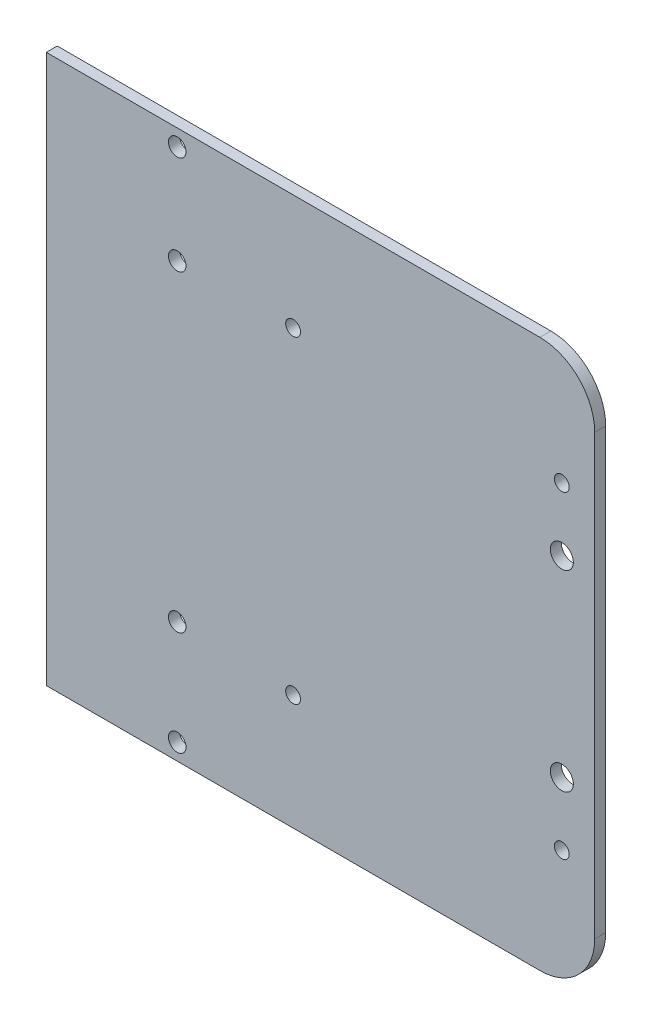
SolidWorks part; units mm, degrees
ref_plane "前视基准面" through (0, 0, 0) normal (0, 0, 1) x (1, 0, 0)
ref_plane "上视基准面" through (0, 0, 0) normal (0, 1, 0) x (1, 0, 0)
ref_plane "右视基准面" through (0, 0, 0) normal (1, 0, 0) x (0, 0, -1)
sketch "草图1" plane through (0, 0, 0) normal (0, 0, 1) x (1, 0, 0)
  line L0 (50, 0) -> (-50, 0) construction
  line L1 (-50, 50) -> (40, 50)
  line L2 (-50, 50) -> (-50, -50)
  line L3 (-50, -50) -> (40, -50)
  line L4 (50, 40) -> (50, -40)
  line L5 (-50, 50) -> (50, -50) construction
  line L6 (-50, -50) -> (50, 50) construction
  arc A2 (40, 50) -> (50, 40) centre (40, 40) cw
  arc A3 (50, -40) -> (40, -50) centre (40, -40) cw
  point P0 (0, 0)
  dimension "D6" = 10
  dimension "D1" = 100
  dimension "D2" = 100
extrude "凸台-拉伸1" add sketch "草图1" along normal blind 2
sketch "草图3" plane through (0, 0, 2) normal (0, 0, 1) x (1, 0, 0)
  line L0 (-50, 0) -> (50, 0) construction
  line L1 (-5, -50) -> (-5, 50) construction
  line L2 (19.5, -50) -> (19.5, 50) construction
  line L3 (44, -50) -> (44, 50) construction
  line L4 (50, -40) -> (50, 40)
  line L5 (40, 50) -> (-50, 50)
  line L6 (-50, 50) -> (-50, -50)
  line L7 (-50, -50) -> (40, -50)
  line L8 (50, -40) -> (50, 40)
  line L9 (40, 50) -> (-50, 50)
  line L10 (-50, 50) -> (-50, -50)
  line L11 (-50, -50) -> (40, -50)
  circle A0 centre (-5, -29) radius 1.35
  circle A1 centre (-5, 29) radius 1.35
  circle A2 centre (44, 29) radius 1.35
  circle A3 centre (44, -29) radius 1.35
  arc A6 (40, -50) -> (50, -40) centre (40, -40) ccw
  arc A7 (40, -50) -> (50, -40) centre (40, -40) ccw
  arc A8 (50, 40) -> (40, 50) centre (40, 40) ccw
  arc A9 (50, 40) -> (40, 50) centre (40, 40) ccw
  dimension "D3" = 2.7
  dimension "D4" = 58
  dimension "D5" = 49
  dimension "D2" = 6
  dimension "D1" = 0
extrude "切除-拉伸1" cut sketch "草图3" against normal through all contours A0 | A1 | A2 | A3
sketch "草图7" plane through (0, 0, 2) normal (0, 0, 1) x (1, 0, 0)
  line L0 (50, 0) -> (-50, 0) construction
  line L1 (44, 50) -> (44, -50) construction
  line L4 (50, -40) -> (50, 40)
  line L5 (40, 50) -> (-50, 50)
  line L6 (-50, 50) -> (-50, -50)
  line L7 (-50, -50) -> (40, -50)
  line L8 (50, -40) -> (50, 40)
  line L9 (40, 50) -> (-50, 50)
  line L10 (-50, 50) -> (-50, -50)
  line L11 (-50, -50) -> (40, -50)
  circle A0 centre (44, 17.5) radius 2.1
  circle A1 centre (44, -17.5) radius 2.1
  arc A4 (40, -50) -> (50, -40) centre (40, -40) ccw
  arc A5 (40, -50) -> (50, -40) centre (40, -40) ccw
  arc A6 (50, 40) -> (40, 50) centre (40, 40) ccw
  arc A7 (50, 40) -> (40, 50) centre (40, 40) ccw
  dimension "D3" = 4.2
  dimension "D4" = 35
  dimension "D2" = 6
  dimension "D1" = 0
extrude "切除-拉伸5" cut sketch "草图7" against normal blind 10 contours A0 | A1
sketch "草图8" plane through (0, 0, 0) normal (0, 0, -1) x (-1, 0, 0)
  line L0 (23.125, 52) -> (23.125, 24) construction
  line L1 (23.125, 24) -> (51, 24) construction
  line L2 (51, 24) -> (51, 52) construction
  line L3 (51, 52) -> (23.125, 52) construction
  line L4 (50, -50) -> (50, 50)
  line L5 (50, 50) -> (-40, 50)
  line L6 (-50, 40) -> (-50, -40)
  line L7 (-40, -50) -> (50, -50)
  line L8 (50, -50) -> (50, 50)
  line L9 (50, 50) -> (-40, 50)
  line L10 (-50, 40) -> (-50, -40)
  line L11 (-40, -50) -> (50, -50)
  line L12 (51, -52) -> (51, -23) construction
  line L13 (51, -23) -> (23.125, -23) construction
  line L14 (23.125, -23) -> (23.125, -52) construction
  line L15 (23.125, -52) -> (51, -52) construction
  line L16 (23.125, 52) -> (23.125, 24)
  line L17 (23.125, 24) -> (51, 24)
  line L18 (51, 24) -> (51, 52)
  line L19 (51, 52) -> (23.125, 52)
  line L20 (51, -52) -> (51, -23)
  line L21 (51, -23) -> (23.125, -23)
  line L22 (23.125, -23) -> (23.125, -52)
  line L23 (23.125, -52) -> (51, -52)
  circle A0 centre (26.125, 29) radius 1.6
  circle A1 centre (26.125, 47) radius 1.6
  arc A2 (-40, 50) -> (-50, 40) centre (-40, 40) ccw
  arc A3 (-50, -40) -> (-40, -50) centre (-40, -40) ccw
  arc A4 (-40, 50) -> (-50, 40) centre (-40, 40) ccw
  arc A5 (-50, -40) -> (-40, -50) centre (-40, -40) ccw
  circle A6 centre (26.125, -28) radius 1.6
  circle A7 centre (26.125, -47) radius 1.6
  dimension "D1" = 0
extrude "切除-拉伸6" cut sketch "草图8" against normal through all contours A7 | A6 | A0 | A1
sketch "草图9" plane through (0, 0, 0) normal (0, 0, -1) x (-1, 0, 0)
  line L0 (-31.975, -49.5062) -> (-25.625, -49.5062) construction
  line L1 (22.125, -23) -> (50, -23)
  line L2 (22.125, -23) -> (22.125, -50)
  line L3 (22.125, -50) -> (50, -50)
  line L4 (50, -50) -> (50, 50)
  line L5 (50, 50) -> (-40, 50)
  line L6 (-50, 40) -> (-50, -40)
  line L7 (-40, -50) -> (50, -50)
  line L8 (50, -50) -> (50, 50)
  line L9 (50, 50) -> (-40, 50)
  line L10 (-50, 40) -> (-50, -40)
  line L11 (-40, -50) -> (50, -50)
  line L12 (50, -23) -> (50, -50)
  line L13 (22.125, 24) -> (50, 24)
  line L14 (22.125, 24) -> (22.125, 50)
  line L15 (22.125, 50) -> (50, 50)
  line L16 (50, 24) -> (50, 50)
  line L18 (-12.875, 37.4938) -> (-6.525, 37.4938)
  line L19 (-12.875, 37.4938) -> (-12.875, 32.9938)
  line L20 (-12.875, 32.9938) -> (-6.525, 32.9938)
  line L21 (-6.525, 37.4938) -> (-6.525, 32.9938)
  line L22 (-31.975, 37.4938) -> (-25.625, 37.4938)
  line L23 (-31.975, 37.4938) -> (-31.975, 32.9938)
  line L24 (-31.975, 32.9938) -> (-25.625, 32.9938)
  line L25 (-25.625, 37.4938) -> (-25.625, 32.9938)
  line L26 (-25.625, -49.5062) -> (-31.975, -49.5062)
  line L27 (-25.625, -49.5062) -> (-25.625, -45.0062)
  line L28 (-25.625, -45.0062) -> (-31.975, -45.0062)
  line L29 (-31.975, -49.5062) -> (-31.975, -45.0062)
  line L30 (-12.875, -45.0062) -> (-6.525, -45.0062)
  line L31 (-12.875, -45.0062) -> (-12.875, -49.5062)
  line L32 (-12.875, -49.5062) -> (-6.525, -49.5062)
  line L33 (-6.525, -45.0062) -> (-6.525, -49.5062)
  circle A1 centre (5, -29) radius 2.65
  arc A2 (-40, 50) -> (-50, 40) centre (-40, 40) ccw
  arc A3 (-50, -40) -> (-40, -50) centre (-40, -40) ccw
  arc A4 (-40, 50) -> (-50, 40) centre (-40, 40) ccw
  arc A5 (-50, -40) -> (-40, -50) centre (-40, -40) ccw
  circle A6 centre (5, 29) radius 2.65
  circle A7 centre (-44, 29) radius 2.65
  circle A8 centre (-44, 17.5) radius 3.5
  circle A9 centre (-44, -17.5) radius 3.5
  circle A10 centre (-44, -29) radius 2.65
  point P18 (-31.975, -45.0062)
  point P39 (-25.625, -49.5062)
  point P40 (-25.625, 32.9938)
  point P43 (-12.875, -45.0062)
  point P44 (-6.525, -49.5062)
  point P45 (-31.975, 37.4938)
  point P46 (-6.525, 32.9938)
  point P47 (-12.875, 37.4938)
  dimension "D1" = 0
